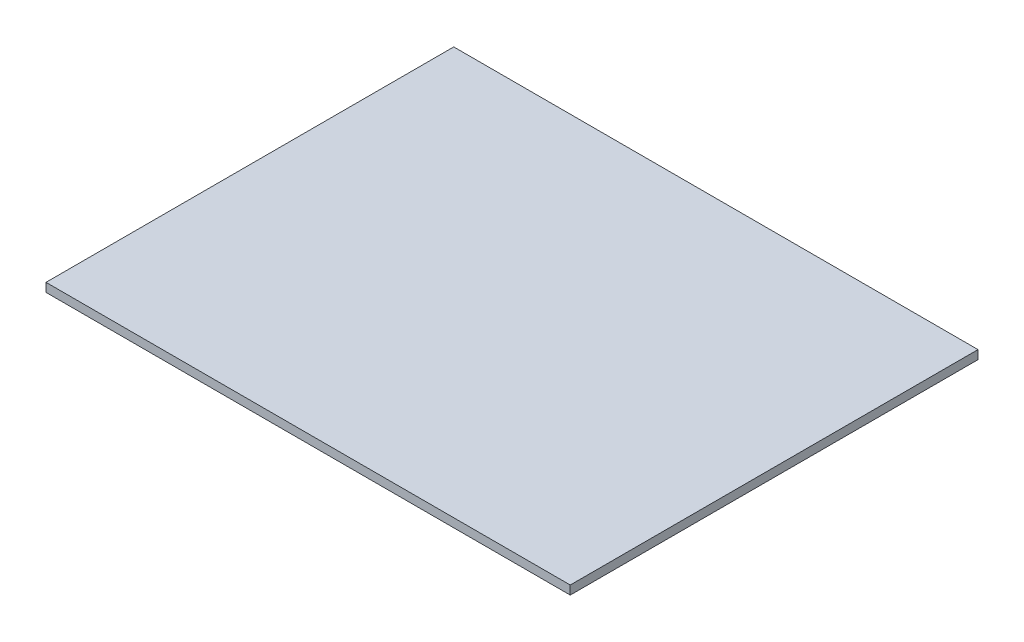
SolidWorks part; units mm, degrees
ref_plane "Front Plane" through (0, 0, 0) normal (0, 0, 1) x (1, 0, 0)
ref_plane "Top Plane" through (0, 0, 0) normal (0, 1, 0) x (1, 0, 0)
ref_plane "Right Plane" through (0, 0, 0) normal (1, 0, 0) x (0, 0, -1)
sketch "Sketch1" plane through (0, 0, 0) normal (0, 1, 0) x (1, 0, 0)
  line L1 (0, 0) -> (90, 0)
  line L2 (0, 0) -> (0, 70)
  line L3 (0, 70) -> (90, 70)
  line L4 (90, 0) -> (90, 70)
  dimension "D1" = 70
  dimension "D2" = 90
extrude "Boss-Extrude1" add sketch "Sketch1" along normal blind 1.5
